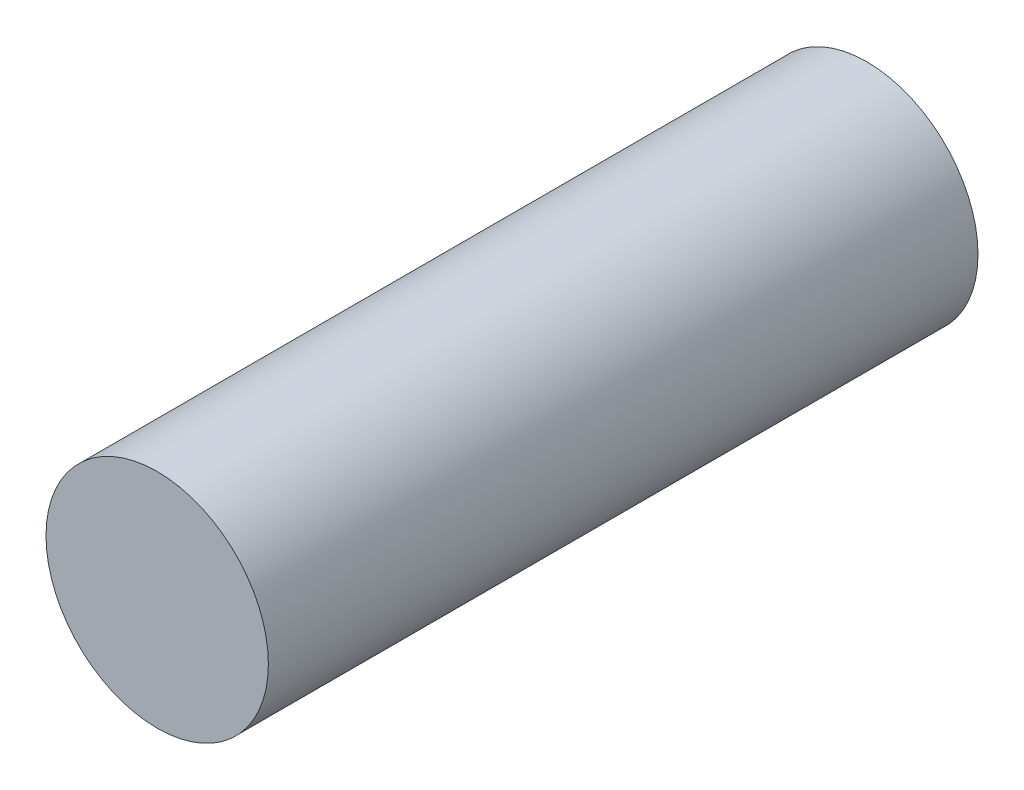
SolidWorks part; units mm, degrees
ref_plane "Vorne" through (0, 0, 0) normal (0, 0, 1) x (1, 0, 0)
ref_plane "Oben" through (0, 0, 0) normal (0, 1, 0) x (1, 0, 0)
ref_plane "Rechts" through (0, 0, 0) normal (1, 0, 0) x (0, 0, -1)
sketch "Skizze1" plane through (0, 0, 0) normal (0, 0, 1) x (1, 0, 0)
  circle A0 centre (0, 0) radius 15.6683
extrude "Aufsatz-Linear austragen1" add sketch "Skizze1" along normal blind 100
ref_plane "Ebene1" through (0, 15.6683, 0) normal (0, 1, 0) x (1, 0, 0)
